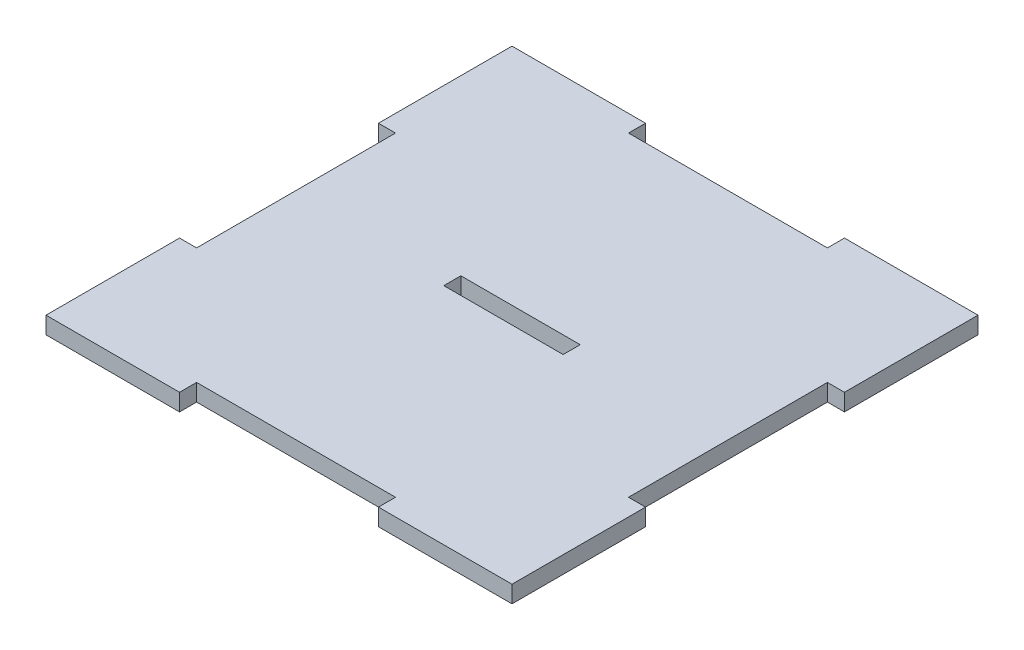
SolidWorks part; units mm, degrees
ref_plane "Front Plane" through (0, 0, 0) normal (0, 0, 1) x (1, 0, 0)
ref_plane "Top Plane" through (0, 0, 0) normal (0, 1, 0) x (1, 0, 0)
ref_plane "Right Plane" through (0, 0, 0) normal (1, 0, 0) x (0, 0, -1)
sketch "Sketch1" plane through (0, 0, 0) normal (0, 1, 0) x (1, 0, 0)
  line L0 (0, 38) -> (0, -38) construction
  line L1 (-41, -41) -> (-17.5, -41)
  line L2 (-41, -41) -> (-41, -17.5)
  line L3 (-41, 41) -> (-17.5, 41)
  line L4 (41, -41) -> (41, -17.5)
  line L5 (-41, -41) -> (41, 41) construction
  line L6 (-41, 41) -> (41, -41) construction
  line L11 (-41, 17.5) -> (-38, 17.5)
  line L12 (-38, 17.5) -> (-38, -17.5)
  line L13 (-35, 0) -> (38, 0) construction
  line L26 (17.5, 41) -> (41, 41)
  line L27 (41, 17.5) -> (41, 41)
  line L28 (17.5, -41) -> (41, -41)
  line L29 (-41, 17.5) -> (-41, 41)
  line L30 (-38, -17.5) -> (-41, -17.5)
  line L31 (-17.5, 41) -> (-17.5, 38)
  line L32 (-17.5, 38) -> (17.5, 38)
  line L33 (17.5, 38) -> (17.5, 41)
  line L34 (41, 17.5) -> (38, 17.5)
  line L35 (38, 17.5) -> (38, -17.5)
  line L36 (38, -17.5) -> (41, -17.5)
  line L37 (17.5, -41) -> (17.5, -38)
  line L38 (17.5, -38) -> (-17.5, -38)
  line L39 (-17.5, -38) -> (-17.5, -41)
  point P0 (0, 0)
  point P6 (0, 0)
  dimension "D1" = 3
  dimension "D2" = 82
  dimension "D3" = 3
  dimension "D4" = 82
  dimension "D5" = 3
  dimension "D6" = 3
extrude "Boss-Extrude1" add sketch "Sketch1" along normal blind 3
sketch "Sketch2" plane through (0, 3, 0) normal (0, 1, 0) x (1, 0, 0)
  line L9 (-10.5, 1.5) -> (10.5, 1.5)
  line L10 (-10.5, 1.5) -> (-10.5, -1.5)
  line L11 (-10.5, -1.5) -> (10.5, -1.5)
  line L12 (10.5, 1.5) -> (10.5, -1.5)
  line L13 (-10.5, 1.5) -> (10.5, -1.5) construction
  line L14 (-10.5, -1.5) -> (10.5, 1.5) construction
  point P0 (0, 0)
  dimension "D1" = 21
  dimension "D2" = 3
extrude "Cut-Extrude1" cut sketch "Sketch2" against normal blind 3
